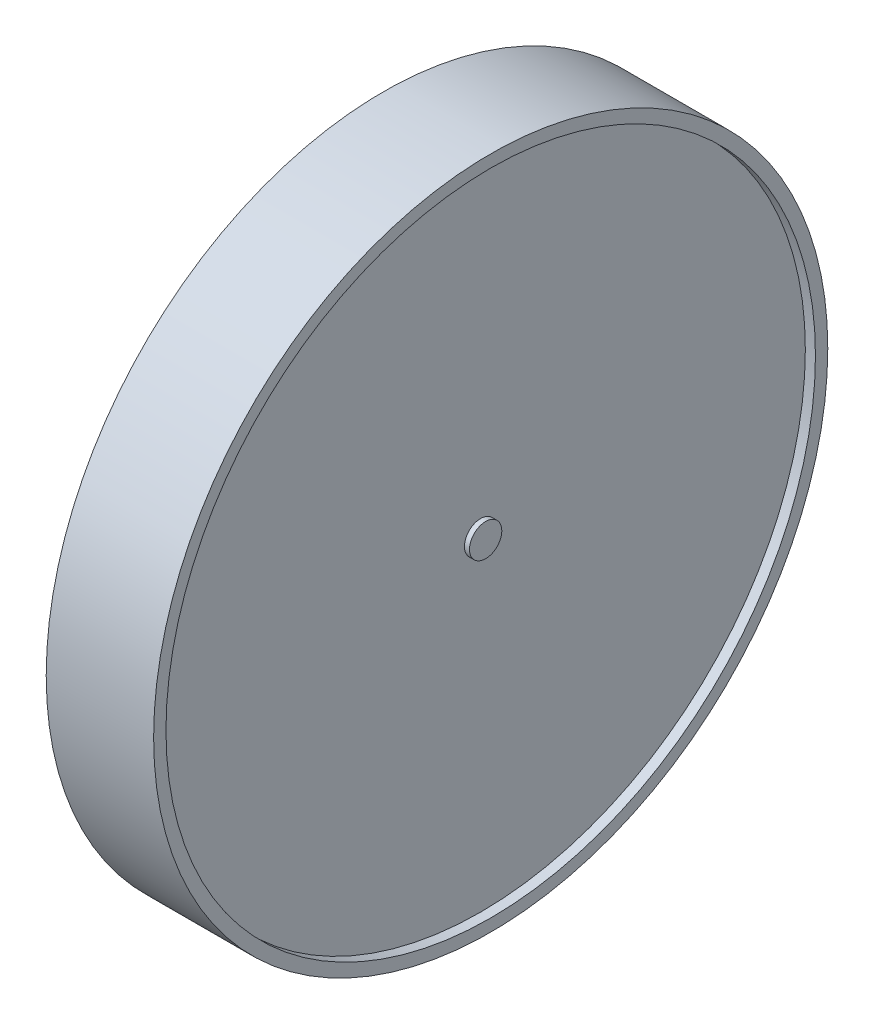
SolidWorks part; units mm, degrees
ref_plane "Alzado" through (0, 0, 0) normal (0, 0, 1) x (1, 0, 0)
ref_plane "Planta" through (0, 0, 0) normal (0, 1, 0) x (1, 0, 0)
ref_plane "Vista lateral" through (0, 0, 0) normal (1, 0, 0) x (0, 0, -1)
sketch "Croquis1" plane through (0, 0, 0) normal (0, 1, 0) x (1, 0, 0)
  line L0 (0, 89.2426) -> (0, -98.8657) construction
  line L1 (-125.0344, 0) -> (132.9877, 0) construction
  line L2 (0, 49.8506) -> (0, -87.2306)
  line L3 (0, -87.2306) -> (45.8804, -87.2306)
  line L4 (45.8804, -87.2306) -> (45.8804, -81.9588)
  line L5 (45.8804, -81.9588) -> (41.5659, -81.9588)
  line L6 (41.5659, -81.9588) -> (41.5659, 49.8506)
  line L7 (41.5659, 49.8506) -> (43.7231, 49.8506)
  line L8 (43.7231, 49.8506) -> (43.7231, 56.746)
  line L9 (43.7231, 56.746) -> (0, 56.746)
  line L10 (0, 49.8506) -> (0, 56.746)
  dimension "D1" = 137.0812
  dimension "D2" = 45.8804
  dimension "D3" = 5.2719
  dimension "D4" = 4.3145
  dimension "D5" = 131.8094
  dimension "D6" = 2.1573
  dimension "D7" = 6.8954
  dimension "D8" = 43.7231
revolve "Revolución1" add sketch "Croquis1" angle 360 about L9
